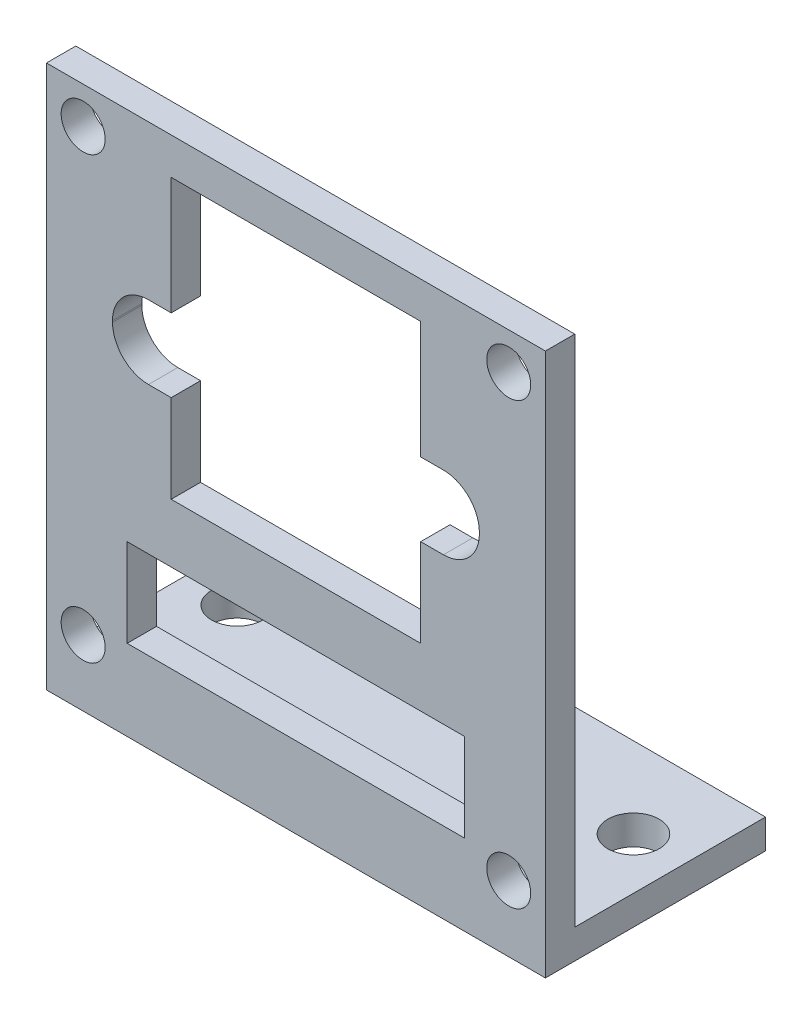
SolidWorks part; units mm, degrees
ref_plane "Plano frontal" through (0, 0, 0) normal (0, 0, 1) x (1, 0, 0)
ref_plane "Plano superior" through (0, 0, 0) normal (0, 1, 0) x (1, 0, 0)
ref_plane "Plano direito" through (0, 0, 0) normal (1, 0, 0) x (0, 0, -1)
sketch "Esboço1" plane through (0, 0, 0) normal (0, 0, 1) x (1, 0, 0)
  line L0 (-13.8103, -1.1707) -> (-13.8103, -7.1707)
  line L1 (-22.3103, 14.3293) -> (11.6897, 14.3293)
  line L2 (-22.3103, 14.3293) -> (-22.3103, -20.6707)
  line L3 (-22.3103, -20.6707) -> (11.6897, -20.6707)
  line L4 (11.6897, 14.3293) -> (11.6897, -20.6707)
  line L5 (-16.8103, -11.1707) -> (6.1897, -11.1707)
  line L6 (-16.8103, -11.1707) -> (-16.8103, -17.1707)
  line L7 (-16.8103, -17.1707) -> (6.1897, -17.1707)
  line L8 (6.1897, -11.1707) -> (6.1897, -17.1707)
  line L9 (-13.8103, 11.8293) -> (3.1897, 11.8293)
  line L10 (-13.8103, 11.8293) -> (-13.8103, 3.8293)
  line L11 (-13.8103, -7.1707) -> (3.1897, -7.1707)
  line L12 (3.1897, 11.8293) -> (3.1897, 3.8293)
  line L13 (-13.8103, 3.8293) -> (-15.3603, 3.8293)
  line L15 (-13.8103, -1.1707) -> (-15.3603, -1.1707)
  line L16 (-17.8103, 1.3793) -> (-17.8103, 1.2793)
  line L17 (3.1897, 3.8293) -> (4.7397, 3.8293)
  line L19 (3.1897, -1.1707) -> (4.7397, -1.1707)
  line L20 (7.1897, 1.3793) -> (7.1897, 1.2793)
  line L21 (3.1897, -1.1707) -> (3.1897, -7.1707)
  circle A0 centre (-19.8103, 11.8293) radius 1.5
  circle A1 centre (9.1897, 11.8293) radius 1.5
  circle A2 centre (-19.8103, -18.1707) radius 1.5
  circle A3 centre (9.1897, -18.1707) radius 1.5
  arc A4 (4.7397, -1.1707) -> (7.1897, 1.2793) centre (4.7397, 1.2793) ccw
  arc A5 (4.7397, 3.8293) -> (7.1897, 1.3793) centre (4.7397, 1.3793) cw
  arc A6 (-15.3603, -1.1707) -> (-17.8103, 1.2793) centre (-15.3603, 1.2793) cw
  arc A7 (-15.3603, 3.8293) -> (-17.8103, 1.3793) centre (-15.3603, 1.3793) ccw
  point P30 (7.1897, -1.1707)
  point P33 (7.1897, 3.8293)
  point P36 (-17.8103, -1.1707)
  point P39 (-17.8103, 3.8293)
  dimension "D5" = 3
  dimension "D22" = 2.45
  dimension "D1" = 35
  dimension "D2" = 34
  dimension "D3" = 2.5
  dimension "D4" = 2.5
  dimension "D8" = 23
  dimension "D9" = 5.5
  dimension "D10" = 6
  dimension "D11" = 3.5
  dimension "D12" = 17
  dimension "D13" = 19
  dimension "D14" = 2.5
  dimension "D15" = 5
  dimension "D16" = 5
  dimension "D17" = 10.5
  dimension "D18" = 10.5
  dimension "D19" = 4
  dimension "D20" = 4
  dimension "D21" = 8.5
  dimension "D6" = 2
  dimension "D7" = 2
extrude "Ressalto-extrusão1" add sketch "Esboço1" along normal blind 2
sketch "Esboço2" plane through (0, 0, 2) normal (0, 0, 1) x (1, 0, 0)
  line L1 (-22.3103, -20.6707) -> (11.6897, -20.6707)
  line L2 (-22.3103, -20.6707) -> (-22.3103, -22.6707)
  line L3 (-22.3103, -22.6707) -> (11.6897, -22.6707)
  line L4 (11.6897, -20.6707) -> (11.6897, -22.6707)
  dimension "D1" = 2
extrude "Ressalto-extrusão2" add sketch "Esboço2" against normal blind 15
sketch "Esboço3" plane through (0, -20.6707, 0) normal (0, 1, 0) x (1, 0, 0)
  line L0 (-22.3103, 13) -> (-22.3103, 0) construction
  line L2 (11.6897, 13) -> (11.6897, 0) construction
  line L3 (11.6897, 13) -> (-5.3103, 13) construction
  line L4 (11.6897, 13) -> (-22.3103, 13) construction
  line L6 (11.6897, 0) -> (-22.3103, 0) construction
  line L8 (-23.7422, 7.5) -> (18.1087, 7.5) construction
  circle A1 centre (8.1897, 7.5) radius 1.75
  circle A2 centre (-18.8103, 7.5) radius 1.75
  dimension "D1" = 5.5
  dimension "D4" = 3.5
  dimension "D5" = 3.5
  dimension "D2" = 3.5
  dimension "D3" = 3.5
extrude "Corte-extrusão1" cut sketch "Esboço3" against normal blind 15
